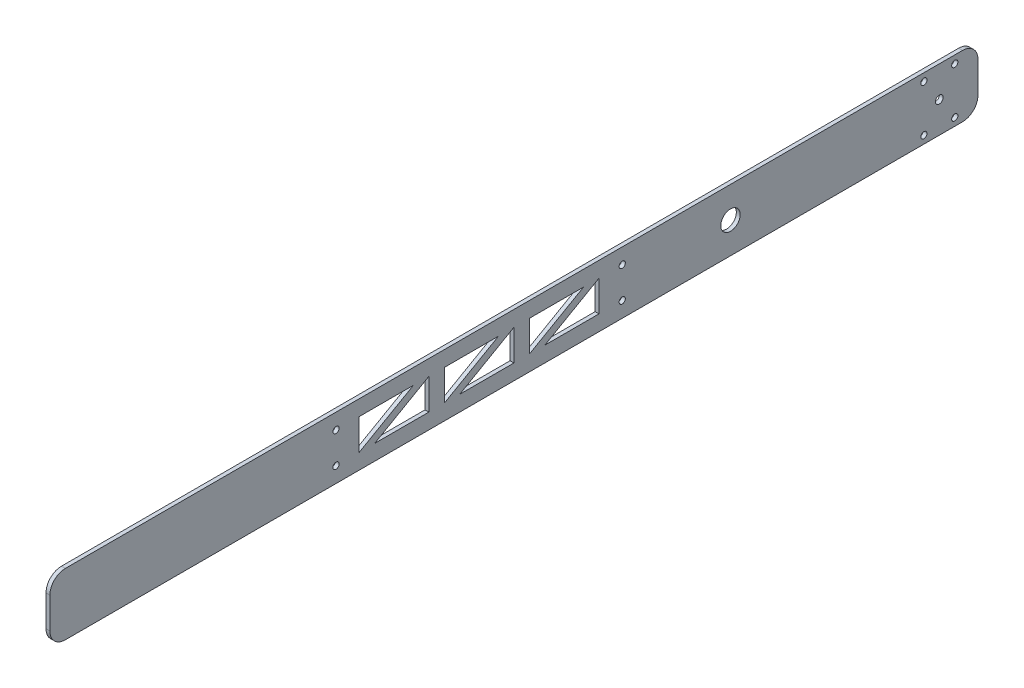
SolidWorks part; units mm, degrees
material "1060 Alloy"
ref_plane "Front Plane" through (0, 0, 0) normal (0, 0, 1) x (1, 0, 0)
ref_plane "Top Plane" through (0, 0, 0) normal (0, 1, 0) x (1, 0, 0)
ref_plane "Right Plane" through (0, 0, 0) normal (1, 0, 0) x (0, 0, -1)
sketch "Sketch1" plane through (0, 0, 0) normal (1, 0, 0) x (0, 0, -1)
  line L0 (177.8, 38.1) -> (177.8, 12.7)
  line L1 (165.1, 0) -> (-571.5, 0)
  line L2 (0, 0) -> (0, 50.8) construction
  line L3 (165.1, 50.8) -> (-571.5, 50.8)
  line L4 (-507.6587, 38.1) -> (372.0993, 38.1) construction
  line L5 (-584.2, 38.1) -> (-584.2, 12.7)
  line L6 (-663.1888, 12.7) -> (-221.2336, 12.7) construction
  line L7 (-190.5, 38.1) -> (-146.05, 38.1)
  line L8 (133.35, 44.45) -> (133.35, 6.35) construction
  line L9 (133.35, 6.35) -> (158.75, 6.35) construction
  line L10 (158.75, 6.35) -> (158.75, 44.45) construction
  line L11 (158.75, 44.45) -> (133.35, 44.45) construction
  line L25 (-349.25, 119.599) -> (-349.25, -64.072) construction
  line L26 (-133.35, 38.1) -> (-133.35, 12.7)
  line L27 (-133.35, 12.7) -> (-177.8, 12.7)
  line L28 (-177.8, 12.7) -> (-133.35, 38.1)
  line L30 (-146.05, 38.1) -> (-190.5, 12.7)
  line L31 (-190.5, 12.7) -> (-190.5, 38.1)
  line L32 (-203.2, 12.7) -> (-203.2, 38.1)
  line L33 (-247.65, 12.7) -> (-203.2, 12.7)
  line L34 (-203.2, 38.1) -> (-247.65, 12.7)
  line L35 (-215.9, 38.1) -> (-260.35, 12.7)
  line L36 (-260.35, 38.1) -> (-215.9, 38.1)
  line L37 (-260.35, 12.7) -> (-260.35, 38.1)
  line L38 (-273.05, 38.1) -> (-273.05, 12.7)
  line L39 (-317.5, 12.7) -> (-273.05, 38.1)
  line L40 (-273.05, 12.7) -> (-317.5, 12.7)
  line L41 (-330.2, 12.7) -> (-330.2, 38.1)
  line L42 (-330.2, 38.1) -> (-285.75, 38.1)
  line L43 (-285.75, 38.1) -> (-330.2, 12.7)
  circle A0 centre (-25.4, 25.4) radius 7.9629
  arc A1 (177.8, 12.7) -> (165.1, 0) centre (165.1, 12.7) cw
  arc A2 (165.1, 50.8) -> (177.8, 38.1) centre (165.1, 38.1) cw
  circle A3 centre (146.05, 25.4) radius 3.175
  circle A4 centre (-349.25, 38.1) radius 2.5527
  circle A5 centre (-349.25, 12.7) radius 2.5527
  circle A6 centre (-114.3, 38.1) radius 2.5527
  circle A7 centre (-114.3, 12.7) radius 2.5527
  circle A8 centre (133.35, 44.45) radius 2.5527
  circle A9 centre (158.75, 44.45) radius 2.5527
  circle A10 centre (158.75, 6.35) radius 2.5527
  arc A11 (-584.2, 12.7) -> (-571.5, 0) centre (-571.5, 12.7) ccw
  arc A12 (-584.2, 38.1) -> (-571.5, 50.8) centre (-571.5, 38.1) cw
  circle A13 centre (133.35, 6.35) radius 2.5527
  point P8 (177.8, 0)
  point P13 (-25.4, 25.4)
  point P14 (177.8, 50.8)
  dimension "D7" = 50.8
  dimension "D8" = 12.7
  dimension "D9" = 12.7
  dimension "D10" = 6.35
  dimension "D11" = 31.75
  dimension "D22" = 5.1054
  dimension "D25" = 12.7
  dimension "D26" = 234.95
  dimension "D23" = 5.1054
  dimension "D24" = 12.7
  dimension "D27" = 19.05
  dimension "D28" = 19.05
  dimension "D33" = 44.45
  dimension "D34" = 44.45
  dimension "D35" = 44.45
  dimension "D36" = 44.45
  dimension "D37" = 44.45
  dimension "D38" = 19.05
  dimension "D39" = 12.7
  dimension "D46" = 12.7
  dimension "D47" = 19.05
  dimension "D48" = 5.1054
  dimension "D13" = 19.05
  dimension "D15" = 12.7
  dimension "D16" = 12.7
  dimension "D17" = 12.7
  dimension "D19" = 15.9258
  dimension "D5" = 762
  dimension "D12" = 25.4
  dimension "D20" = 88.9
  dimension "D21" = 88.9
  dimension "D14" = 44.45
  dimension "D42" = 5.1054
  dimension "D43" = 5.1054
  dimension "D49" = 5.1054
  dimension "D50" = 5.1054
  dimension "D51" = 5.1054
  dimension "D2" = 25.4
  dimension "D3" = 177.8
  dimension "D4" = 25.4
  dimension "D6" = 0
  dimension "D18" = 12.7
  dimension "D29" = 12.7
  dimension "D30" = 12.7
  dimension "D31" = 12.7
  dimension "D32" = 25.4
  dimension "D40" = 12.7
  dimension "D41" = 12.7
  dimension "D44" = 25.4
  dimension "D45" = 38.1
extrude "Boss-Extrude1" add sketch "Sketch1" along normal blind 3.175
